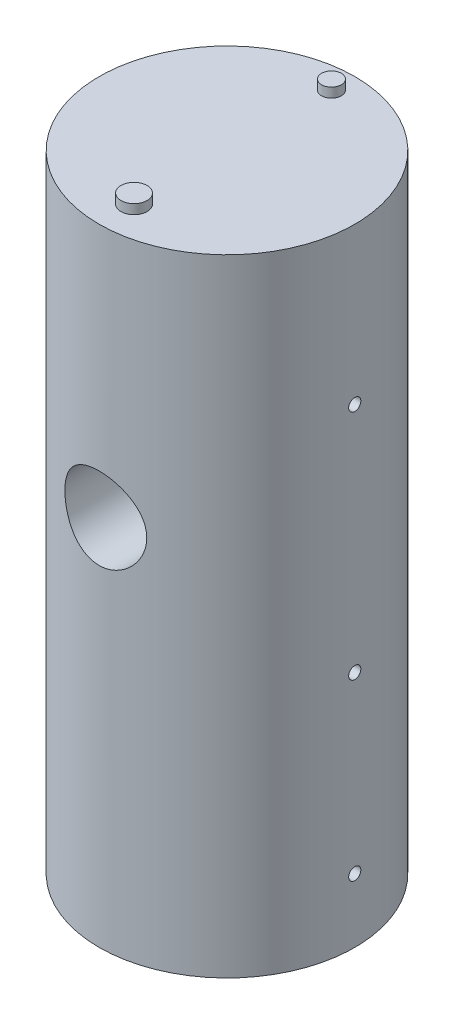
SolidWorks part; units mm, degrees
ref_plane "Front Plane" through (0, 0, 0) normal (0, 0, 1) x (1, 0, 0)
ref_plane "Top Plane" through (0, 0, 0) normal (0, 1, 0) x (1, 0, 0)
ref_plane "Right Plane" through (0, 0, 0) normal (1, 0, 0) x (0, 0, -1)
sketch "Sketch1" plane through (0, 0, 0) normal (0, 1, 0) x (1, 0, 0)
  circle A0 centre (0, 0) radius 50.8
  dimension "D1" = 101.6
extrude "Boss-Extrude1" add sketch "Sketch1" along normal blind 248.79
ref_plane "Plane1" through (0, 0, 50.8) normal (0, 0, 1) x (1, 0, 0)
ref_plane "Plane2" through (50.8, 0, 0) normal (1, 0, 0) x (0, 0, -1)
sketch "Sketch3" plane through (0, 0, 50.8) normal (0, 0, 1) x (1, 0, 0)
  line L0 (0, 0) -> (0, 147.668) construction
  circle A0 centre (0, 147.668) radius 16.256
  dimension "D1" = 147.668
  dimension "D2" = 32.512
extrude "Cut-Extrude1" cut sketch "Sketch3" against normal blind 25.4
sketch "Sketch4" plane through (50.8, 0, 0) normal (1, 0, 0) x (0, 0, -1)
  line L0 (0, 0) -> (0, 25.4) construction
  line L1 (0, 0) -> (0, 94.58) construction
  line L2 (0, 0) -> (0, 186.79) construction
  circle A0 centre (0, 186.79) radius 2.413
  circle A1 centre (0, 94.58) radius 2.413
  circle A2 centre (0, 25.4) radius 2.413
  dimension "D4" = 4.826
  dimension "D5" = 4.826
  dimension "D6" = 4.826
  dimension "D1" = 25.4
  dimension "D2" = 94.58
  dimension "D3" = 186.79
extrude "Cut-Extrude2" cut sketch "Sketch4" against normal through all
sketch "Sketch5" plane through (0, 248.79, 0) normal (0, 1, 0) x (1, 0, 0)
  circle A0 centre (0, 41.4896) radius 3.936
  circle A1 centre (0, -36.9187) radius 5.1862
extrude "Boss-Extrude2" add sketch "Sketch5" along normal blind 3.81
